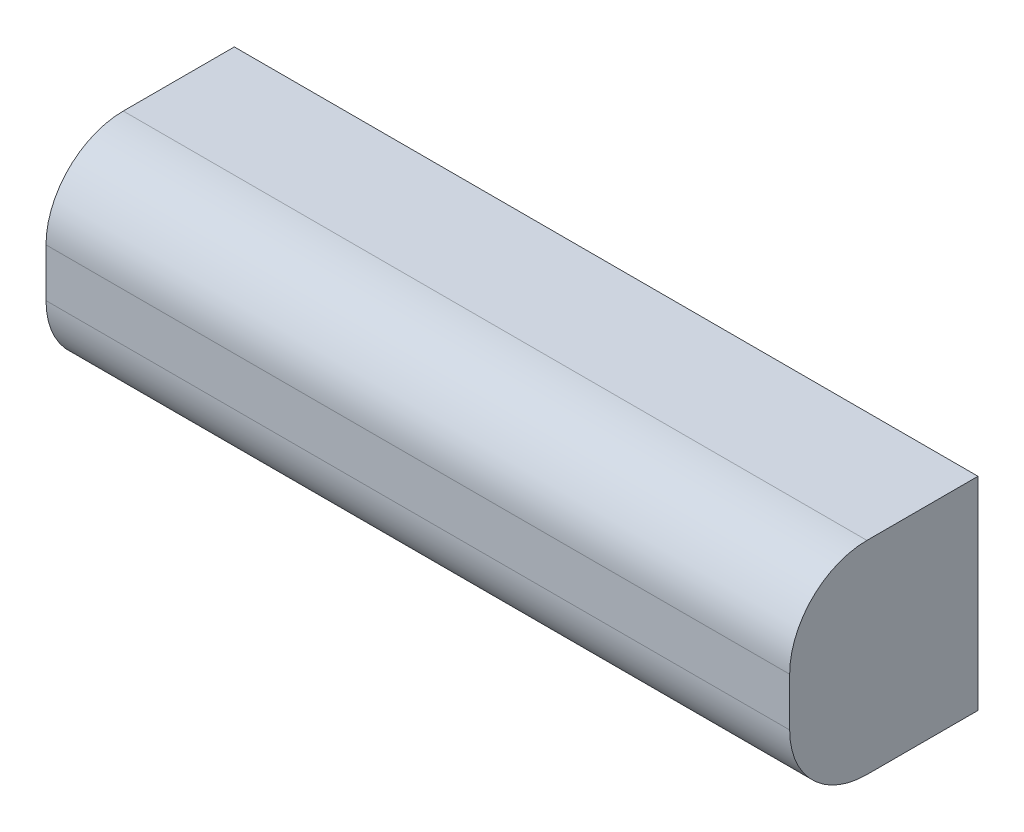
SolidWorks part; units mm, degrees
ref_plane "Přední rovina" through (0, 0, 0) normal (0, 0, 1) x (1, 0, 0)
ref_plane "Horní rovina" through (0, 0, 0) normal (0, 1, 0) x (1, 0, 0)
ref_plane "Pravá rovina" through (0, 0, 0) normal (1, 0, 0) x (0, 0, -1)
sketch "Skica1" plane through (0, 0, 0) normal (0, 0, 1) x (1, 0, 0)
  line L1 (-38.5, -10.5) -> (38.5, -10.5)
  line L2 (-38.5, -10.5) -> (-38.5, 10.5)
  line L3 (-38.5, 10.5) -> (38.5, 10.5)
  line L4 (38.5, -10.5) -> (38.5, 10.5)
  line L5 (-38.5, -10.5) -> (38.5, 10.5) construction
  line L6 (-38.5, 10.5) -> (38.5, -10.5) construction
  point P0 (0, 0)
  dimension "D1" = 77
  dimension "D2" = 21
extrude "Přidat vysunutím1" add sketch "Skica1" along normal blind 19.5
fillet "Zaoblit1" radius 8 2 edges at (0, 10.5, 19.5) (0, -10.5, 19.5)
